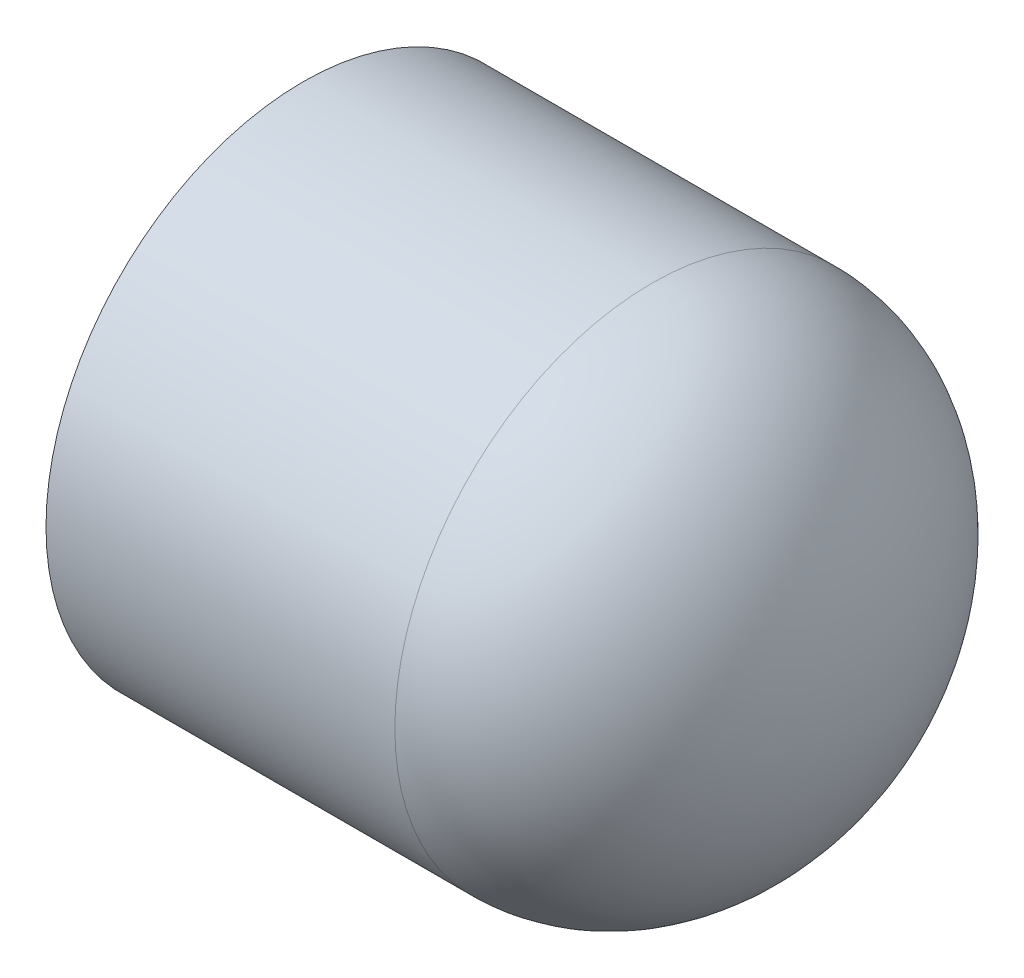
SolidWorks part; units mm, degrees
ref_plane "Front Plane" through (0, 0, 0) normal (0, 0, 1) x (1, 0, 0)
ref_plane "Top Plane" through (0, 0, 0) normal (0, 1, 0) x (1, 0, 0)
ref_plane "Right Plane" through (0, 0, 0) normal (1, 0, 0) x (0, 0, -1)
sketch "Sketch0" plane through (0, 0, 0) normal (0, 0, 1) x (1, 0, 0)
  line L3 (-22.0091, 0) -> (22.0091, 0) construction
  line L4 (-22.0091, 20.5867) -> (-22.0091, -20.5867) construction
  line L5 (5.9309, 16.637) -> (-22.0091, 16.8275) construction
  line L6 (5.9309, 16.637) -> (5.9309, -16.637) construction
  line L7 (5.9309, -16.637) -> (-22.0091, -16.8275) construction
  line L8 (-22.0091, 16.8275) -> (-22.0091, -16.8275) construction
  line L14 (5.9309, 13.3223) -> (5.9309, -13.3223) construction
  point P0 (5.9309, 0)
  dimension "H" = 16.0782
  dimension "M" = 41.1734
  dimension "OD A" = 33.655
  dimension "OD B" = 33.274
  dimension "ID" = 26.6446
  dimension "L" = 44.0182
  dimension "C" = 27.94
sketch "Sketch1" plane through (0, 0, 0) normal (0, 0, 1) x (1, 0, 0)
  line L1 (-22.0091, 0) -> (22.0091, 0) construction
  line L2 (-22.0091, 0) -> (22.0091, 0) construction
  line L3 (18.0594, 0) -> (22.0091, 0)
  line L4 (-22.0091, -20.5867) -> (-22.0091, -16.8275)
  line L5 (-22.0091, -16.8275) -> (5.9309, -16.637)
  line L6 (5.9309, -16.637) -> (5.9309, -20.5867) construction
  line L9 (5.9309, -20.5867) -> (-22.0091, -20.5867)
  ellipse E2 centre (5.9309, 0) end of major axis (5.9309, 20.5867) minor radius 16.0782 (5.9309, -20.5867) -> (22.0091, 0) ccw
  ellipse E3 centre (5.9309, 0) end of major axis (5.9309, -16.637) minor radius 12.1285 (5.9309, -16.637) -> (18.0594, 0) ccw
revolve "Revolve1" add sketch "Sketch1" angle 360 about L1
